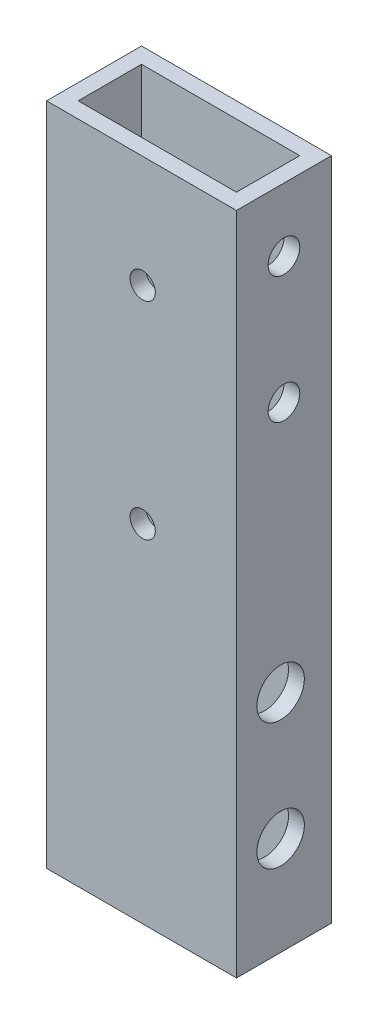
SolidWorks part; units mm, degrees
ref_plane "Front Plane" through (0, 0, 0) normal (0, 0, 1) x (1, 0, 0)
ref_plane "Top Plane" through (0, 0, 0) normal (0, 1, 0) x (1, 0, 0)
ref_plane "Right Plane" through (0, 0, 0) normal (1, 0, 0) x (0, 0, -1)
sketch "Sketch1" plane through (0, 0, 0) normal (0, 1, 0) x (1, 0, 0)
  line L0 (3.175, 15.875) -> (34.925, 15.875)
  line L1 (0, 0) -> (38.1, 0)
  line L2 (0, 0) -> (0, 19.05)
  line L3 (0, 19.05) -> (38.1, 19.05)
  line L4 (38.1, 0) -> (38.1, 19.05)
  line L5 (34.925, 3.175) -> (34.925, 15.875)
  line L6 (3.175, 3.175) -> (34.925, 3.175)
  line L7 (3.175, 3.175) -> (3.175, 15.875)
  dimension "D1" = 38.1
  dimension "D2" = 19.05
extrude "Boss-Extrude1" add sketch "Sketch1" along normal blind 133.35
sketch "Sketch2" plane through (38.1, 0, 0) normal (1, 0, 0) x (0, 0, -1)
  circle A0 centre (9.525, 95.25) radius 3.175 construction
  circle A1 centre (9.525, 95.25) radius 3.175
  circle A2 centre (9.525, 120.65) radius 3.175 construction
  circle A3 centre (9.525, 120.65) radius 3.175
extrude "Cut-Extrude1" cut sketch "Sketch2" against normal through all
sketch "Sketch3" plane through (0, 0, 0) normal (-1, 0, 0) x (0, 0, 1)
  circle A0 centre (-8.8564, 19.7898) radius 2.0193 construction
  circle A1 centre (-8.8564, 19.7898) radius 2.0193
  circle A2 centre (-8.8564, 45.1898) radius 2.0193 construction
  circle A3 centre (-8.8564, 45.1898) radius 2.0193
extrude "Cut-Extrude2" cut sketch "Sketch3" against normal through all
sketch "Sketch4" plane through (34.925, 0, 0) normal (-1, 0, 0) x (0, 0, 1)
  circle A0 centre (-8.8564, 45.1898) radius 4.7625
  circle A1 centre (-8.8564, 19.7898) radius 4.7625
  dimension "D1" = 9.525
extrude "Cut-Extrude3" cut sketch "Sketch4" against normal up to next
sketch "Sketch5" plane through (0, 0, -19.05) normal (0, 0, -1) x (-1, 0, 0)
  circle A0 centre (-19.2722, 69.4912) radius 2.54 construction
  circle A1 centre (-19.2722, 69.4912) radius 2.54
  circle A2 centre (-19.2722, 110.9456) radius 2.54 construction
  circle A3 centre (-19.2722, 110.9456) radius 2.54
extrude "Cut-Extrude4" cut sketch "Sketch5" against normal through all
